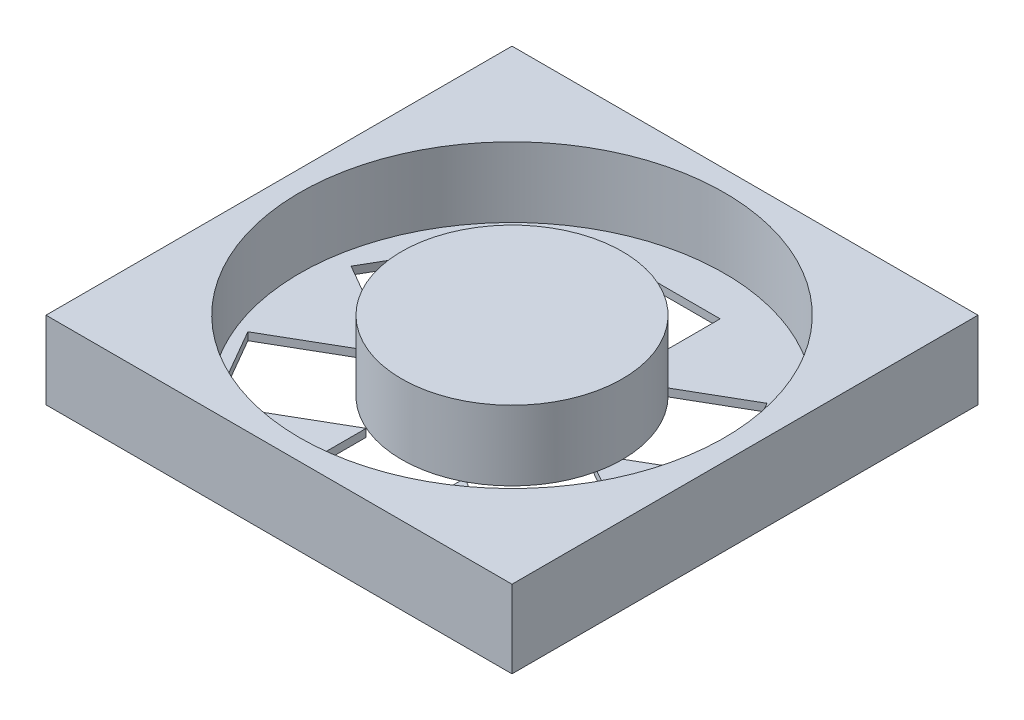
SolidWorks part; units mm, degrees
ref_plane "Front Plane" through (0, 0, 0) normal (0, 0, 1) x (1, 0, 0)
ref_plane "Top Plane" through (0, 0, 0) normal (0, 1, 0) x (1, 0, 0)
ref_plane "Right Plane" through (0, 0, 0) normal (1, 0, 0) x (0, 0, -1)
sketch "Sketch1" plane through (0, 0, 0) normal (0, 1, 0) x (1, 0, 0)
  line L1 (-33.5833, 7) -> (26.4167, 7)
  line L2 (-33.5833, 7) -> (-33.5833, -53)
  line L3 (-33.5833, -53) -> (26.4167, -53)
  line L4 (26.4167, 7) -> (26.4167, -53)
  dimension "D1" = 60
  dimension "D2" = 60
extrude "Boss-Extrude1" add sketch "Sketch1" along normal blind 10
sketch "Sketch2" plane through (0, 10, 0) normal (0, 1, 0) x (1, 0, 0)
  line L0 (-33.5833, -53) -> (26.4167, -53) construction
  line L1 (26.4167, -53) -> (26.4167, 7) construction
  circle A0 centre (-3.5833, -23) radius 27.3391
  circle A1 centre (-3.5833, -23) radius 14.2095
  dimension "D1" = 30
  dimension "D2" = 30
extrude "Cut-Extrude1" cut sketch "Sketch2" against normal blind 9
sketch "Sketch3" plane through (0, 0, 0) normal (0, -1, 0) x (1, 0, 0)
  line L0 (14.325, 42.019) -> (-0.5793, 33.414)
  line L1 (-9.3519, 49.5799) -> (2.5676, 49.5799)
  line L2 (-9.3519, 49.5799) -> (-9.3519, 32.3699)
  line L3 (-9.3519, 32.3699) -> (2.5676, 32.3699)
  line L4 (2.5676, 49.5799) -> (2.5676, 32.3699)
  line L5 (14.325, 42.019) -> (20.2847, 31.6964)
  line L6 (20.2847, 31.6964) -> (5.3805, 23.0914)
  line L7 (-0.5793, 33.414) -> (5.3805, 23.0914)
  line L8 (19.6155, 17.7337) -> (4.7112, 26.3387)
  line L9 (19.6155, 17.7337) -> (13.6557, 7.4111)
  line L10 (13.6557, 7.4111) -> (-1.2486, 16.0161)
  line L11 (4.7112, 26.3387) -> (-1.2486, 16.0161)
  line L12 (1.2291, 1.0094) -> (1.2291, 18.2194)
  line L13 (1.2291, 1.0094) -> (-10.6904, 1.0094)
  line L14 (-10.6904, 1.0094) -> (-10.6904, 18.2194)
  line L15 (1.2291, 18.2194) -> (-10.6904, 18.2194)
  line L16 (-22.4478, 8.5704) -> (-7.5435, 17.1754)
  line L17 (-22.4478, 8.5704) -> (-28.4075, 18.893)
  line L18 (-28.4075, 18.893) -> (-13.5032, 27.498)
  line L19 (-7.5435, 17.1754) -> (-13.5032, 27.498)
  line L20 (-27.7382, 32.8556) -> (-12.834, 24.2506)
  line L21 (-27.7382, 32.8556) -> (-21.7785, 43.1782)
  line L22 (-21.7785, 43.1782) -> (-6.8742, 34.5732)
  line L23 (-12.834, 24.2506) -> (-6.8742, 34.5732)
  point P27 (-4.0614, 25.2947)
  dimension "D1" = 6
extrude "Cut-Extrude3" cut sketch "Sketch3" against normal blind 1 contours L8 L11 L10 L9 | L6 L7 L0 L5 | L4 L3 L2 L1 | L20 L23 L22 L21 | L18 L19 L16 L17 | L14 L15 L12 L13
